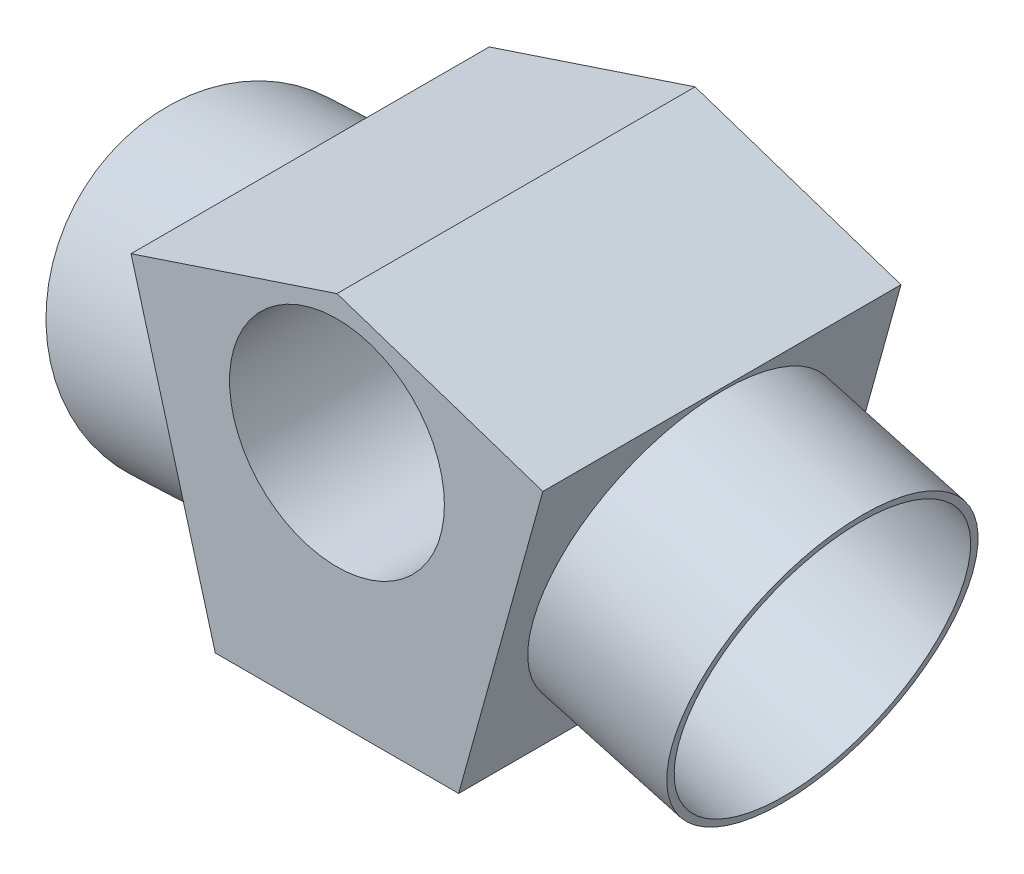
SolidWorks part; units mm, degrees
material "ABS"
ref_plane "Front Plane" through (0, 0, 0) normal (0, 0, 1) x (1, 0, 0)
ref_plane "Top Plane" through (0, 0, 0) normal (0, 1, 0) x (1, 0, 0)
ref_plane "Right Plane" through (0, 0, 0) normal (1, 0, 0) x (0, 0, -1)
sketch "Sketch2" plane through (0, 0, 0) normal (0, 0, 1) x (1, 0, 0)
  line L0 (0, 9.0224) -> (-14.3743, 4.2487)
  line L1 (-14.3743, 4.2487) -> (-8.495, -16.9512)
  line L2 (-8.495, -16.9512) -> (8.495, -16.9512)
  line L3 (0, -55) -> (0, 55) construction
  line L4 (14.3743, 4.2487) -> (8.495, -16.9512)
  line L5 (0, 9.0224) -> (14.3743, 4.2487)
  circle A0 centre (0, 0) radius 7.5
  point P10 (0, -16.9512)
  dimension "D1" = 15
  dimension "D2" = 105.5
extrude "Boss-Extrude1" add sketch "Sketch2" against normal blind 25
sketch "Sketch13" plane through (-12.2536, -3.3982, 0) normal (-0.9636, -0.2672, 0) x (0, 0, 1)
  line L0 (-12.5, 7.9355) -> (-12.5, -14.0645) construction
  line L1 (-25, 7.9355) -> (0, 7.9355) construction
  line L2 (-25, -14.0645) -> (0, -14.0645) construction
ref_plane "Plane6" through (-8.9816, -2.4908, 2.1589) normal (0.9388, 0.2603, -0.2257) x (0.2672, -0.9636, 0)
sketch "Sketch14" plane through (-8.9816, -2.4908, 2.1589) normal (0.9388, 0.2603, -0.2257) x (0.2672, -0.9636, 0)
  line L0 (-7.9355, 15.0471) -> (14.0645, 15.0471) construction
  circle A0 centre (3.0645, 15.0471) radius 10
  point P4 (3.0645, 15.0471)
  dimension "D1" = 20
extrude "Extrude-Thin3" add sketch "Sketch14" against normal blind 12 and the other way blind 3 thin
ref_plane "Plane4" through (20, 0, 0) normal (1, 0, 0) x (0, 0, -1)
sketch "Sketch7" plane through (20, 0, 0) normal (1, 0, 0) x (0, 0, -1)
  line L0 (0, -13.1465) -> (25, -13.1465) construction
  line L1 (0, -16.9512) -> (0, 4.2487) construction
  line L2 (25, -16.9512) -> (25, 4.2487) construction
ref_plane "Plane5" through (21.9571, -6.0893, 0) normal (0.9636, -0.2672, 0) x (0, 0, -1)
sketch "Sketch8" plane through (21.9571, -6.0893, 0) normal (0.9636, -0.2672, 0) x (0, 0, -1)
  circle A0 centre (12.3158, -2.8196) radius 10
  dimension "D1" = 20
extrude "Cut-Extrude4" cut sketch "Sketch8" against normal blind 13 contours A0
sketch "Sketch12" plane through (21.9571, -6.0893, 0) normal (0.9636, -0.2672, 0) x (0, 0, -1)
  circle A0 centre (12.3158, -2.8196) radius 10
extrude "Extrude-Thin2" add sketch "Sketch12" against normal blind 12 thin
mirror "Mirror1" about plane through (0, 0, -25) normal (0, 0, -1) of bodies 107
delete or keep bodies "Body-Delete/Keep 1" type delete bodies bodies 107
